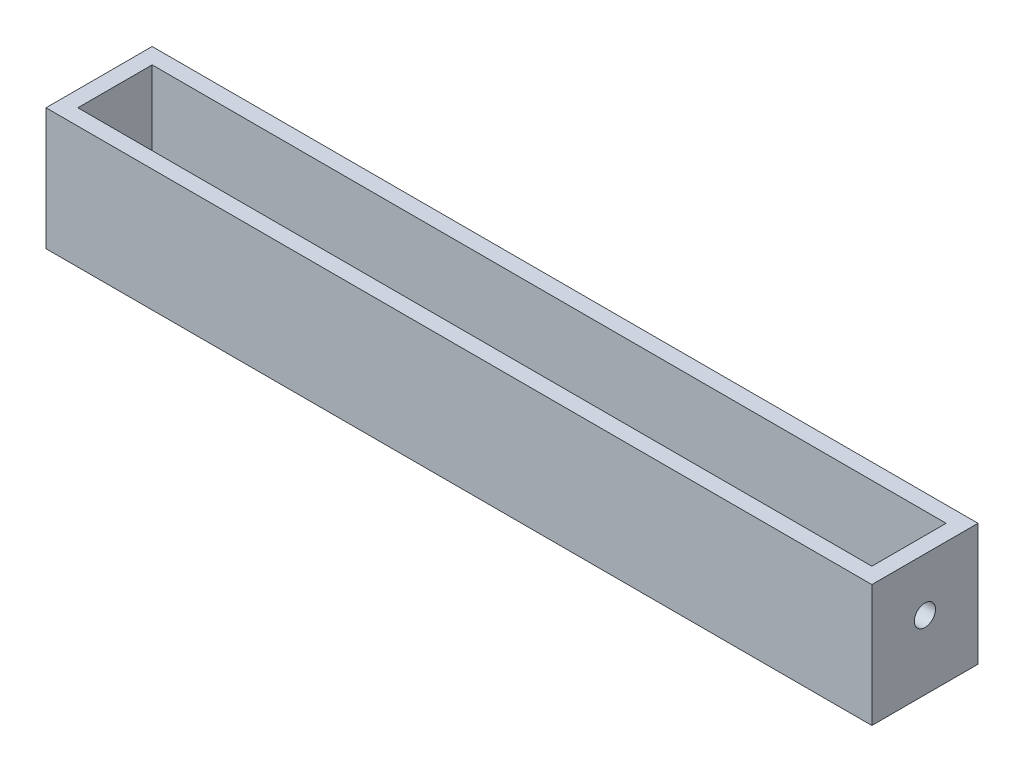
SolidWorks part; units mm, degrees
ref_plane "前视基准面" through (0, 0, 0) normal (0, 0, 1) x (1, 0, 0)
ref_plane "上视基准面" through (0, 0, 0) normal (0, 1, 0) x (1, 0, 0)
ref_plane "右视基准面" through (0, 0, 0) normal (1, 0, 0) x (0, 0, -1)
sketch "草图1" plane through (0, 0, 0) normal (0, 1, 0) x (1, 0, 0)
  line L0 (-77.8, 0) -> (-37.5, 0)
  line L1 (-77.8, -10) -> (77.8, -10)
  line L2 (-77.8, -10) -> (-77.8, 10)
  line L3 (-77.8, 10) -> (77.8, 10)
  line L4 (77.8, -10) -> (77.8, 10)
  line L5 (-77.8, -10) -> (77.8, 10) construction
  line L6 (-77.8, 10) -> (77.8, -10) construction
  line L7 (77.8, 0) -> (37.5, 0)
  circle A0 centre (-37.5, 0) radius 4
  circle A1 centre (37.5, 0) radius 4
  point P0 (0, 0)
  dimension "D1" = 155.6
  dimension "D2" = 20
extrude "凸台-拉伸1" add sketch "草图1" along normal blind 3
sketch "草图2" plane through (0, 3, 0) normal (0, 1, 0) x (1, 0, 0)
  line L1 (-77.8, -10) -> (77.8, -10)
  line L2 (-77.8, -10) -> (-77.8, 10)
  line L3 (-77.8, 10) -> (77.8, 10)
  line L4 (77.8, -10) -> (77.8, 10)
  line L5 (-77.8, -10) -> (77.8, 10) construction
  line L6 (-77.8, 10) -> (77.8, -10) construction
  line L7 (-74.8, -7) -> (74.8, -7)
  line L8 (-74.8, -7) -> (-74.8, 7)
  line L9 (-74.8, 7) -> (74.8, 7)
  line L10 (74.8, -7) -> (74.8, 7)
  line L11 (-74.8, -7) -> (74.8, 7) construction
  line L12 (-74.8, 7) -> (74.8, -7) construction
  point P0 (0, 0)
  point P7 (0, 0)
  line M11 (-77.8, -10) -> (77.8, -10)
  line M12 (77.8, -10) -> (77.8, 10)
  line M13 (77.8, 10) -> (-77.8, 10)
  line M14 (-77.8, 10) -> (-77.8, -10)
extrude "凸台-拉伸2" add sketch "草图2" along normal blind 20 contours L10 L7 L8 L9 M14 M11 M12 M13
sketch "草图3" plane through (-77.8, 0, 0) normal (-1, 0, 0) x (0, 0, 1)
  line L0 (0, 23) -> (0, 13)
  line L1 (-10, 23) -> (10, 23) construction
  circle A0 centre (0, 13) radius 2
extrude "切除-拉伸1" cut sketch "草图3" against normal blind 160
